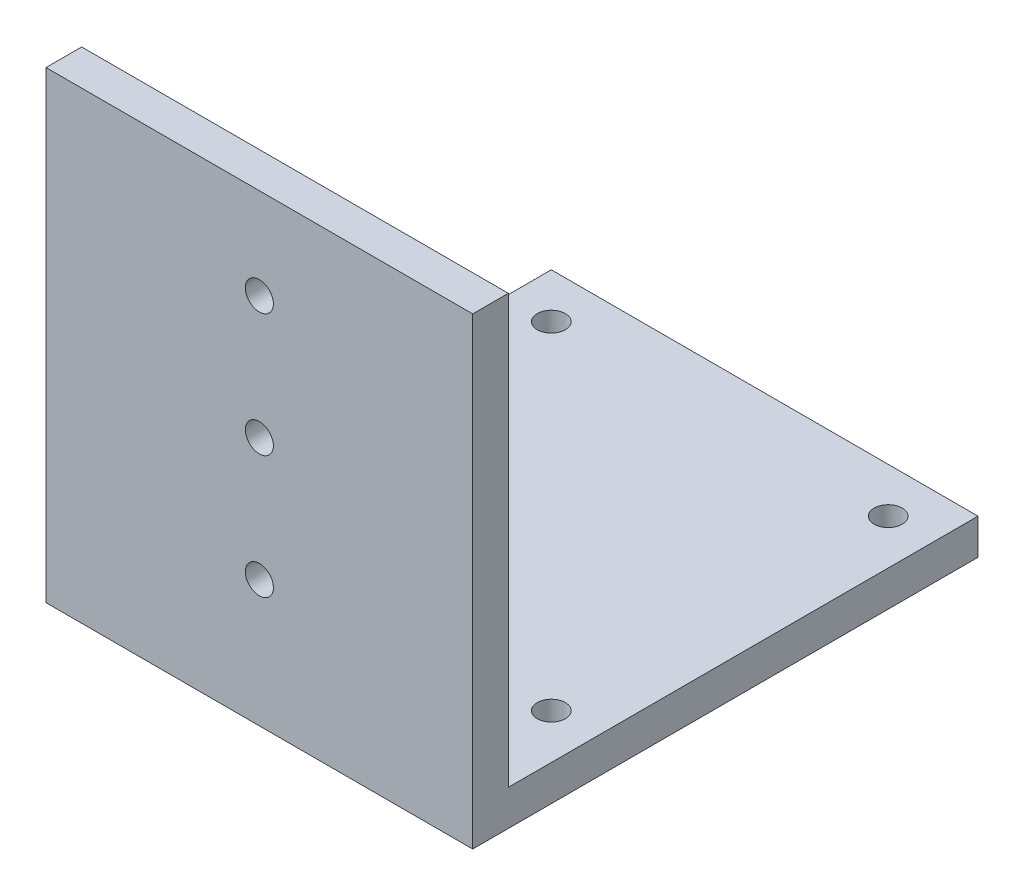
SolidWorks part; units mm, degrees
ref_plane "Front" through (0, 0, 0) normal (0, 0, 1) x (1, 0, 0)
ref_plane "Top" through (0, 0, 0) normal (0, 1, 0) x (1, 0, 0)
ref_plane "Right" through (0, 0, 0) normal (1, 0, 0) x (0, 0, -1)
sketch "Sketch1" plane through (0, 0, 0) normal (0, 1, 0) x (1, 0, 0)
  line L1 (0, 0) -> (38, 0)
  line L2 (0, 0) -> (0, -45)
  line L3 (0, -45) -> (38, -45)
  line L4 (38, 0) -> (38, -45)
  dimension "D1" = 38
  dimension "D2" = 45
extrude "Boss-Extrude1" add sketch "Sketch1" along normal blind 3.175
sketch "Sketch2" plane through (0, 3.175, 0) normal (0, 1, 0) x (1, 0, 0)
  line L0 (38, -45) -> (38, 0) construction
  line L1 (0, -45) -> (38, -45)
  line L2 (0, -45) -> (0, -41.825)
  line L3 (0, -41.825) -> (38, -41.825)
  line L4 (38, -45) -> (38, -41.825)
  dimension "D1" = 3.175
extrude "Boss-Extrude2" add sketch "Sketch2" along normal blind 38.1
sketch "Sketch3" plane through (0, 0, 0) normal (0, -1, 0) x (1, 0, 0)
  line L0 (0, 0) -> (0, 45) construction
  line L1 (38, 45) -> (38, 0) construction
  line L3 (38, 0) -> (0, 0) construction
  circle A0 centre (4, 34) radius 1.25
  circle A1 centre (34, 34) radius 1.25
  circle A2 centre (4, 4) radius 1.25
  circle A4 centre (34, 4) radius 1.25
  dimension "D1" = 2.5
  dimension "D2" = 2.5
  dimension "D3" = 2.5
  dimension "D4" = 2.5
  dimension "D5" = 4
  dimension "D6" = 4
  dimension "D7" = 4
  dimension "D8" = 4
  dimension "D9" = 4
  dimension "D10" = 4
  dimension "D11" = 34
  dimension "D12" = 34
extrude "camera holes" cut sketch "Sketch3" against normal blind 10
sketch "Sketch4" plane through (0, 0, 45) normal (0, 0, 1) x (1, 0, 0)
  line L0 (38, 41.275) -> (0, 41.275) construction
  line L2 (0, 41.275) -> (0, 3.175) construction
  line L3 (38, 3.175) -> (0, 3.175) construction
  circle A1 centre (19, 11.2812) radius 1.25
  circle A2 centre (19, 33.1687) radius 1.25
  circle A3 centre (19, 22.225) radius 1.25
  dimension "D1" = 2.5
  dimension "D2" = 19
  dimension "D3" = 8.1062
  dimension "D4" = 10.9437
  dimension "D5" = 8.1062
extrude "mounting holes" cut sketch "Sketch4" against normal blind 10
